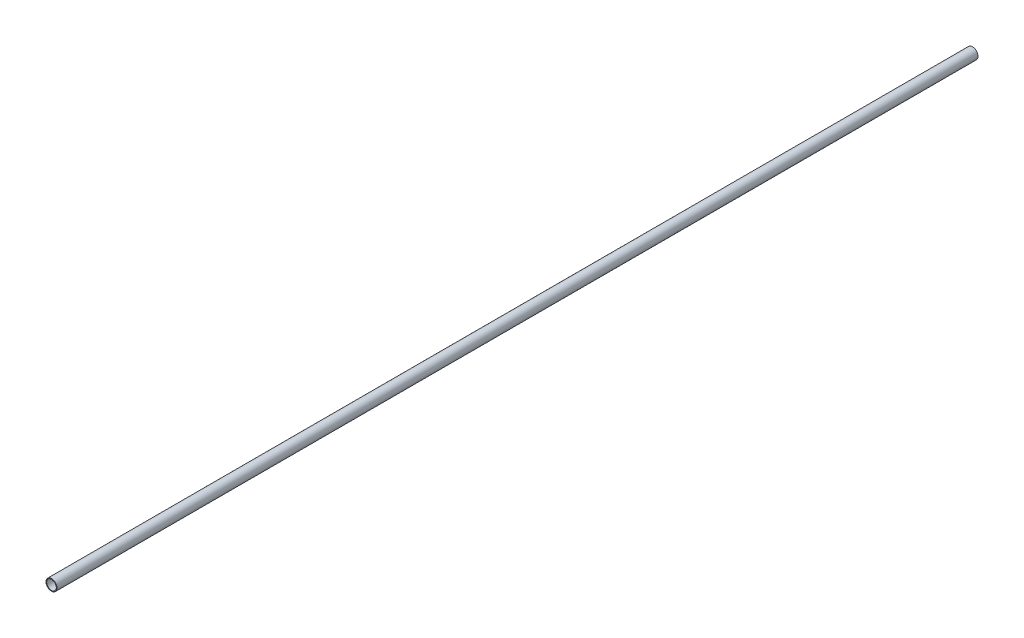
SolidWorks part; units mm, degrees
material "McMaster Carbon Fiber Twill Tube"
ref_plane "Front Plane" through (0, 0, 0) normal (0, 0, 1) x (1, 0, 0)
ref_plane "Top Plane" through (0, 0, 0) normal (0, 1, 0) x (1, 0, 0)
ref_plane "Right Plane" through (0, 0, 0) normal (1, 0, 0) x (0, 0, -1)
sketch "Sketch1" plane through (0, 0, 0) normal (0, 0, 1) x (1, 0, 0)
  circle A0 centre (0, 0) radius 10.922 construction
  circle A1 centre (0, 0) radius 9.525 construction
  point P4 (9.525, 0)
  point P5 (10.922, 0)
  dimension "OD" = 21.844
  dimension "ID" = 19.05
  dimension "Wall Thickness" = 1.397
sketch "Sketch2" plane through (0, 0, 0) normal (1, 0, 0) x (0, 0, -1)
  line L0 (-914.4, 0) -> (914.4, 0) construction
  line L1 (-914.4, -10.922) -> (-914.4, 10.922) construction
  line L2 (-914.4, 10.922) -> (914.4, 10.922) construction
  line L3 (914.4, -10.922) -> (914.4, 10.922) construction
  line L5 (-914.4, -10.922) -> (914.4, -10.922) construction
  point P0 (-892.556, 0)
  point P3 (0, 0)
  point P7 (0, 10.922)
  point P8 (892.556, 0)
  point P11 (-914.4, 0)
  point P13 (914.4, 0)
  dimension "Length" = 1828.8
  dimension "D1" = 21.844
  dimension "D2" = 21.844
sketch "Sketch3" plane through (0, 0, 0) normal (0, 0, 1) x (1, 0, 0)
  circle A0 centre (0, 0) radius 9.525 construction
  circle A1 centre (0, 0) radius 10.922 construction
  circle A2 centre (0, 0) radius 9.525
  circle A3 centre (0, 0) radius 10.922
extrude "Boss-Extrude1" add sketch "Sketch3" along normal up to vertex (914.4 mm away) and the other way up to vertex (914.4 mm away) up to point (0, 0, 914.4) other way up to point (0, 0, -914.4)
equation "\"D1@Sketch2\"=\"OD@Sketch1\""
equation "\"D2@Sketch2\"=\"D1@Sketch2\""
